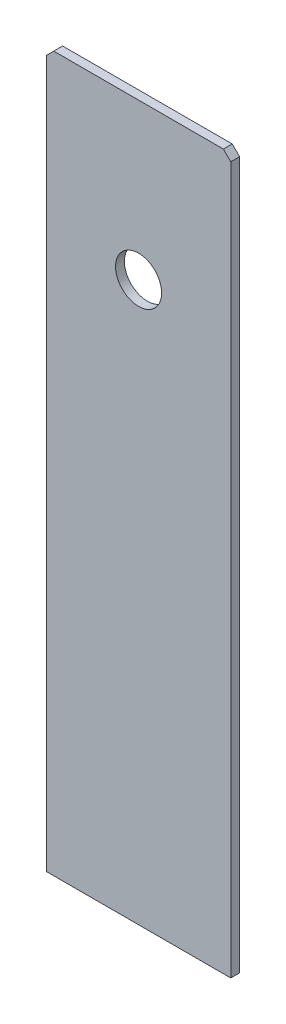
SolidWorks part; units mm, degrees
material "6061 Alloy"
ref_plane "Front Plane" through (0, 0, 0) normal (0, 0, 1) x (1, 0, 0)
ref_plane "Top Plane" through (0, 0, 0) normal (0, 1, 0) x (1, 0, 0)
ref_plane "Right Plane" through (0, 0, 0) normal (1, 0, 0) x (0, 0, -1)
sketch "Sketch1" plane through (0, 0, 0) normal (0, 0, 1) x (1, 0, 0)
  line L0 (31.75, 0) -> (31.75, 192.3796) construction
  line L1 (0, 0) -> (63.5, 0)
  line L2 (0, 0) -> (0, 245.9736)
  line L3 (0, 245.9736) -> (63.5, 245.9736)
  line L4 (63.5, 0) -> (63.5, 245.9736)
  line L5 (8.382, 215.7476) -> (55.118, 215.7476) construction
  line L6 (3.556, 220.5736) -> (59.944, 220.5736) construction
  line L7 (3.556, 220.5736) -> (3.556, 164.1856) construction
  line L8 (3.556, 164.1856) -> (59.944, 164.1856) construction
  line L9 (59.944, 220.5736) -> (59.944, 164.1856) construction
  line L10 (3.556, 220.5736) -> (59.944, 164.1856) construction
  line L11 (3.556, 164.1856) -> (59.944, 220.5736) construction
  line L12 (55.118, 215.7476) -> (55.118, 169.0116) construction
  line L13 (8.382, 169.0116) -> (55.118, 169.0116) construction
  line L14 (8.382, 215.7476) -> (8.382, 169.0116) construction
  line L15 (20.3517, 102.0699) -> (20.3518, 51.3842) construction
  line L16 (43.1482, 108.5723) -> (43.1483, 59.5249) construction
  line L17 (43.1483, 59.5249) -> (63.5, 59.5249) construction
  line L18 (12.5285, 0) -> (12.5285, 18.0677) construction
  line L19 (50.9715, 0) -> (50.9715, 26.3499) construction
  circle A0 centre (8.382, 215.7476) radius 2.413 construction
  circle A1 centre (55.118, 215.7476) radius 2.413 construction
  circle A2 centre (8.382, 169.0116) radius 2.413 construction
  circle A3 centre (55.118, 169.0116) radius 2.413 construction
  circle A4 centre (20.3517, 102.0699) radius 1.9177 construction
  circle A5 centre (43.1482, 108.5723) radius 1.9177 construction
  circle A6 centre (31.75, 192.3796) radius 7.9375
  circle A7 centre (20.3518, 51.3842) radius 1.9177 construction
  circle A8 centre (43.1483, 59.5249) radius 1.9177 construction
  dimension "D4" = 4.826
  dimension "D7" = 3.8354
  dimension "D10" = 15.875
  dimension "D12" = 51.3842
  dimension "D1" = 63.5
  dimension "D2" = 56.388
  dimension "D3" = 4.826
  dimension "D5" = 25.4
  dimension "D6" = 192.3796
  dimension "D8" = 102.0699
  dimension "D9" = 7.8232
  dimension "D11" = 19.2215
  dimension "D13" = 59.5249
  dimension "D14" = 108.5723
  dimension "D15" = 19.2215
  dimension "D16" = 7.8232
extrude "Boss-Extrude1" add sketch "Sketch1" along normal blind 3.048
fillet "Fillet1" [suppressed] radius 19.05
ref_plane "Plane1" through (31.75, 0, 0) normal (1, 0, 0) x (0, 0, -1)
chamfer "Chamfer1" distance 2.54 angle 45 2 edges at (0, 245.9736, 1.524) (63.5, 245.9736, 1.524)
equation "\"bolt diameter\" = 0.2"
equation "\"stepper body width\" = 2.22"
equation "\"stepper mount offset\" = 0.19"
equation "\"stepper mount diameter\" = 0.19"
equation "\"D2@Sketch1\"=\"stepper body width\""
equation "\"D3@Sketch1\"=\"stepper mount offset\""
equation "\"D4@Sketch1\"=\"stepper mount diameter\""
equation "\"thin metal\" = 0.12"
equation "\"thick metal\" = 0.25"
equation "\"y axis stepper wall bracket thickness\" = 1"
equation "\"y axis stepper wall mount side offset\" = 1/2"
equation "\"y axis stepper wall mount top offset\" = 1/2"
equation "\"y axis stepper wall width\" = \"stepper body width\" + 1                  "
equation "\"y axis stepper wall height off base\" = 8"
equation "\"D6@Sketch1\"=0.454 -0.255 + 2 * \"thin metal\" + \"recognizer arm height to hole\" + 2 + \"recognizer nut plate height\" / 2 + 0.255"
equation "\"base length\" = 21"
equation "\"stepper shaft offset from body\" = 0.79"
equation "\"recognizer width\" = 2.5"
equation "\"recognizer nut plate height\" = 1.25"
equation "\"base width\" = 16.5"
equation "\"glass pane length\" = 14.125"
equation "\"glass pane width\" = 10.1875"
equation "\"glass pane wall width\" = 3/4"
equation "\"glass lip\" = 1/4"
equation "\"stepper spacer thickness\" = 0.2"
equation "\"recognizer nut plate offset\" = 1.5"
equation "\"recognizer bracket length\" = 4"
equation "\"recognizer arm height to hole\"= 4.255"
equation "\"x axis threaded rod length\" = 3"
